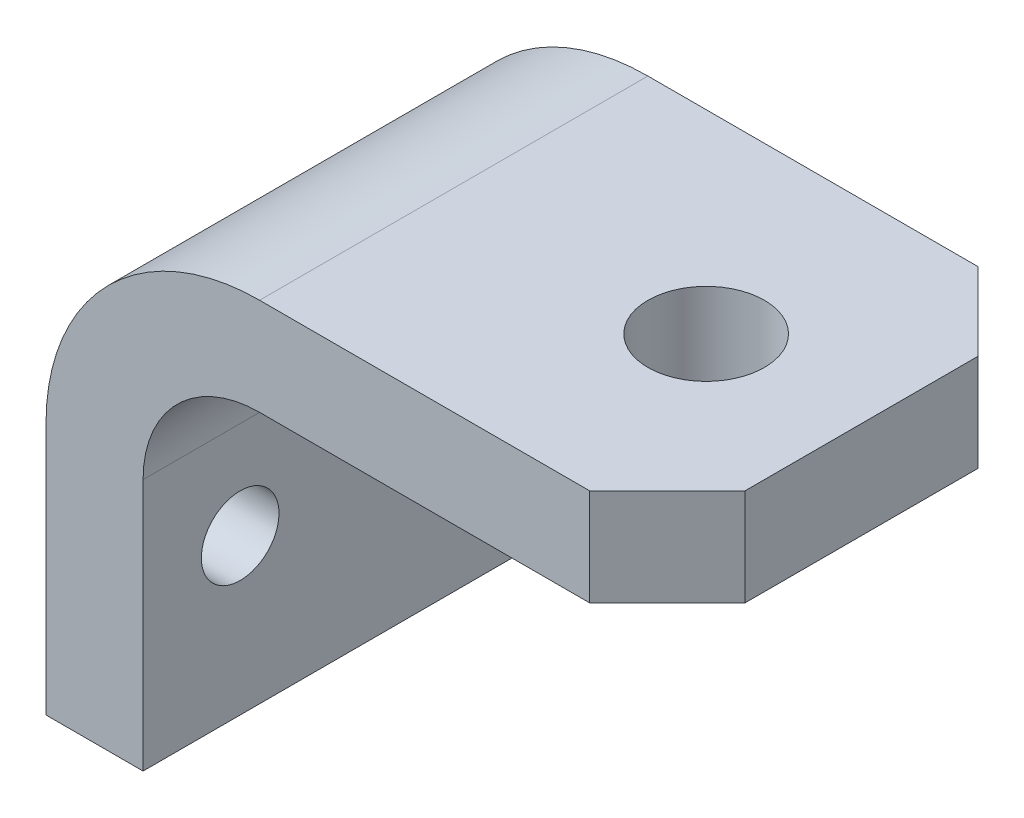
SolidWorks part; units mm, degrees
material "Alloy Steel"
ref_plane "Front" through (0, 0, 0) normal (0, 0, 1) x (1, 0, 0)
ref_plane "Top" through (0, 0, 0) normal (0, 1, 0) x (1, 0, 0)
ref_plane "Right" through (0, 0, 0) normal (1, 0, 0) x (0, 0, -1)
sketch "Sketch1" plane through (0, 0, 0) normal (0, 0, 1) x (1, 0, 0)
  line L0 (-76.2, -60.325) -> (-76.2, -19.05)
  line L1 (25.4, 15.875) -> (-41.275, 15.875)
  line L2 (-76.2, -60.325) -> (-60.325, -60.325)
  line L3 (-60.325, -60.325) -> (-60.325, -19.05)
  line L4 (25.4, 0) -> (-41.275, 0)
  line L5 (25.4, 0) -> (25.4, 15.875)
  arc A0 (-41.275, 0) -> (-60.325, -19.05) centre (-41.275, -19.05) ccw
  arc A1 (-41.275, 15.875) -> (-76.2, -19.05) centre (-41.275, -19.05) ccw
  dimension "D3" = 19.05
  dimension "D4" = 15.875
  dimension "D1" = 101.6
  dimension "D2" = 76.2
  dimension "D5" = 25.4
extrude "Hitch Profile for Extrusion" add sketch "Sketch1" along normal mid plane 63.5
sketch "Sketch2" plane through (0, 15.875, 0) normal (0, 1, 0) x (1, 0, 0)
  circle A0 centre (0, 0) radius 9.525
  dimension "D1" = 19.05
extrude "Ball Anchor hole" cut sketch "Sketch2" against normal through all
sketch "Sketch3" plane through (0, 15.875, 0) normal (0, 1, 0) x (1, 0, 0)
  line L0 (12.7, 31.75) -> (25.4, 19.05)
  line L1 (25.4, 31.75) -> (-41.275, 31.75) construction
  line L2 (25.4, -31.75) -> (25.4, 31.75) construction
  line L3 (12.7, -31.75) -> (25.4, -19.05)
  line L4 (25.4, -31.75) -> (-41.275, -31.75) construction
  line L5 (12.7, 31.75) -> (25.4, 31.75)
  line L6 (25.4, 31.75) -> (25.4, 19.05)
  line L7 (25.4, -19.05) -> (25.4, -31.75)
  line L8 (25.4, -31.75) -> (12.7, -31.75)
  dimension "D1" = 12.7
  dimension "D2" = 12.7
  dimension "D3" = 45
  dimension "D4" = 45
extrude "45 Deg Corners" cut sketch "Sketch3" against normal through all
sketch "Sketch4" plane through (-60.325, 0, 0) normal (1, 0, 0) x (0, 0, -1)
  line L0 (-19.05, 15.875) -> (19.05, 15.875) construction
  line L1 (-31.75, -60.325) -> (-31.75, -19.05) construction
  circle A0 centre (-15.875, -34.925) radius 6.35
  circle A1 centre (15.875, -34.925) radius 6.35
  dimension "D1" = 12.7
  dimension "D2" = 50.8
  dimension "D3" = 50.8
  dimension "D4" = 15.875
  dimension "D5" = 31.75
extrude "Bolt Hole x 2" cut sketch "Sketch4" against normal up to next
